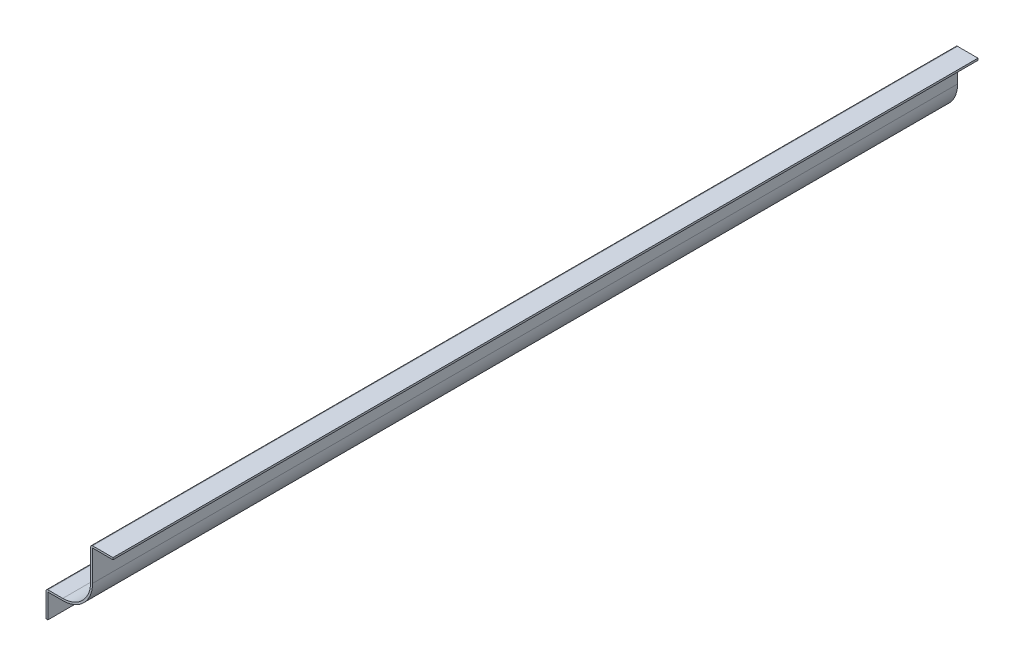
SolidWorks part; units mm, degrees
ref_plane "Front Plane" through (0, 0, 0) normal (0, 0, 1) x (1, 0, 0)
ref_plane "Top Plane" through (0, 0, 0) normal (0, 1, 0) x (1, 0, 0)
ref_plane "Right Plane" through (0, 0, 0) normal (1, 0, 0) x (0, 0, -1)
sketch "Sketch1" plane through (0, 0, 0) normal (0, 0, 1) x (1, 0, 0)
  line L0 (0, 0) -> (0, 22.225)
  line L1 (0, 22.225) -> (14.2875, 22.225)
  line L2 (38.1, 46.0375) -> (38.1, 73.8188)
  line L3 (38.1, 73.8188) -> (57.15, 73.8187)
  arc A0 (14.2875, 22.225) -> (38.1, 46.0375) centre (14.2875, 46.0375) ccw
  dimension "D2" = 23.8125
  dimension "D1" = 22.225
  dimension "D3" = 19.05
  dimension "D4" = 73.8188
  dimension "D5" = 38.1
extrude "Extrude-Thin1" add sketch "Sketch1" against normal blind 738.1875 thin
fillet "Fillet1" radius 1.651 2 edges at (38.1, 73.8188, -369.0938) (0, 22.225, -369.0938)
